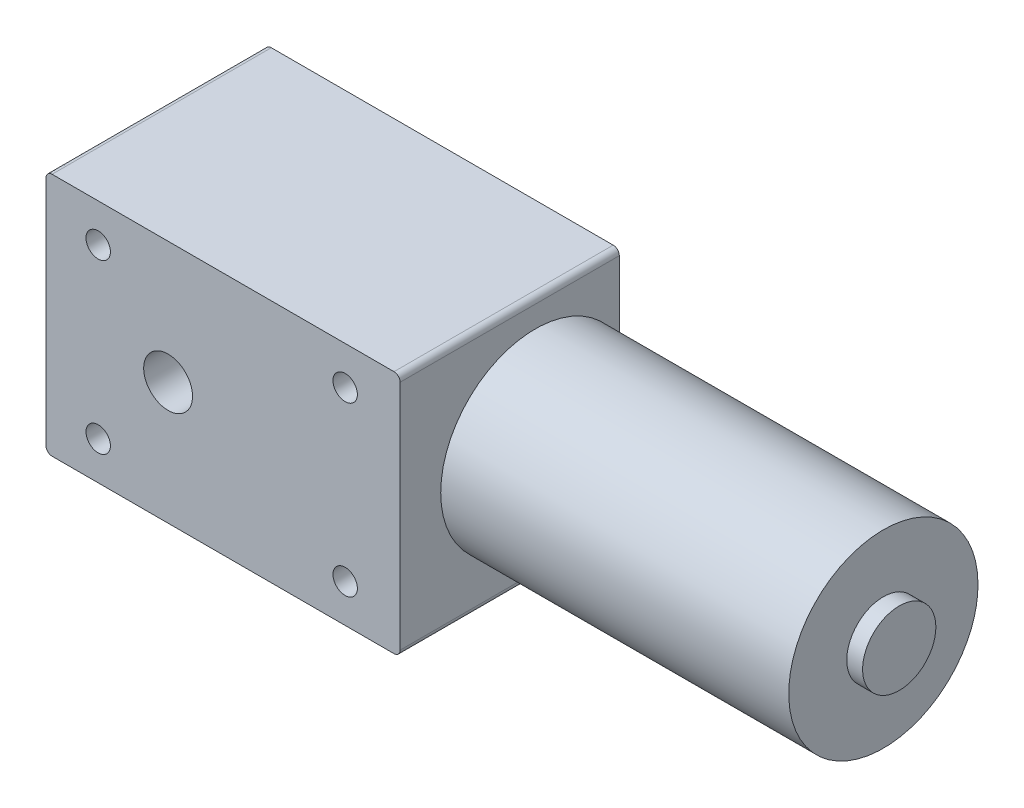
SolidWorks part; units mm, degrees
material "1100-H26 棒材(SS)"
ref_plane "Front Plane" through (0, 0, 0) normal (0, 0, 1) x (1, 0, 0)
ref_plane "Top Plane" through (0, 0, 0) normal (0, 1, 0) x (1, 0, 0)
ref_plane "Right Plane" through (0, 0, 0) normal (1, 0, 0) x (0, 0, -1)
sketch "Sketch1" plane through (0, 0, 0) normal (1, 0, 0) x (0, 0, -1)
  circle A0 centre (0, 0) radius 15.5
  dimension "D1" = 31
extrude "Boss-Extrude1" add sketch "Sketch1" along normal blind 57
sketch "Sketch2" plane through (57, 0, 0) normal (1, 0, 0) x (0, 0, -1)
  circle A0 centre (0, 0) radius 6
  dimension "D1" = 12
extrude "Boss-Extrude2" add sketch "Sketch2" along normal blind 2.6
sketch "Sketch3" plane through (0, 0, 0) normal (0, 0, 1) x (1, 0, 0)
  line L0 (0, 15.5) -> (0, -15.5) construction
  line L1 (-58, -20) -> (0, -20)
  line L2 (-58, -20) -> (-58, 20)
  line L3 (-58, 20) -> (0, 20)
  line L4 (0, -20) -> (0, 20)
  line L5 (-58, -20) -> (0, 20) construction
  line L6 (-58, 20) -> (0, -20) construction
  line L7 (-9, 13.75) -> (-49.45, 13.75) construction
  line L8 (-9, 13.75) -> (-9, -13.75) construction
  line L9 (0, 0) -> (-38, 0) construction
  circle A0 centre (-9, 13.75) radius 2
  circle A1 centre (-49.45, 13.75) radius 2
  circle A2 centre (-49.45, -13.75) radius 2
  circle A3 centre (-9, -13.75) radius 2
  circle A4 centre (-38, 0) radius 4
  point P0 (-29, 0)
  dimension "D3" = 4
  dimension "D4" = 2
  dimension "D8" = 8
  dimension "D11" = 20
  dimension "D1" = 58
  dimension "D2" = 40
  dimension "D6" = 40.45
  dimension "D7" = 27.5
  dimension "D9" = 13.75
  dimension "D10" = 9
  dimension "D5" = 2
extrude "Boss-Extrude3" add sketch "Sketch3" along normal blind 22.15 and the other way blind 13.75
fillet "Fillet1" radius 1 4 edges at (0, -20, 4.2) (-58, -20, 4.2) (-58, 20, 4.2) (0, 20, 4.2)
